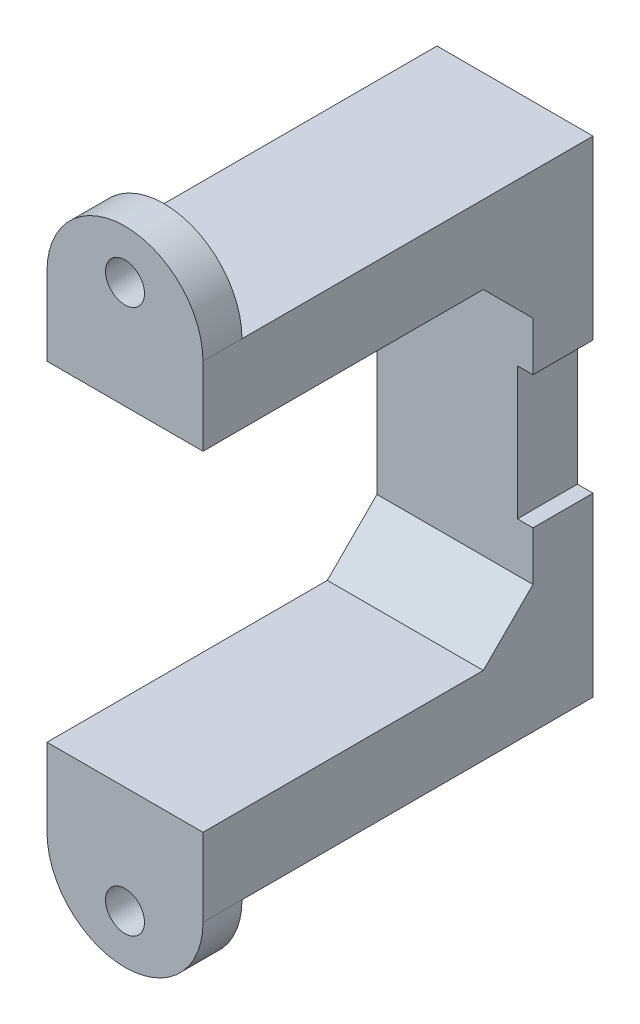
SolidWorks part; units mm, degrees
ref_plane "Ebene vorne" through (0, 0, 0) normal (0, 0, 1) x (1, 0, 0)
ref_plane "Ebene oben" through (0, 0, 0) normal (0, 1, 0) x (1, 0, 0)
ref_plane "Ebene rechts" through (0, 0, 0) normal (1, 0, 0) x (0, 0, -1)
sketch "Sketch1" plane through (0, 0, 0) normal (0, 1, 0) x (1, 0, 0)
  line L0 (-20, 0) -> (0, 0)
  line L2 (0, 0) -> (0, 50)
  line L3 (0, 50) -> (-20, 50)
  line L4 (-20, 0) -> (-20, 50)
  point P0 (0, 0)
  dimension "D1" = 20
  dimension "D2" = 50
extrude "Boss-Extrude2" add sketch "Sketch1" along normal blind 62.3
sketch "Sketch2" plane through (0, 0, 0) normal (1, 0, 0) x (0, 0, -1)
  line L1 (0, 52.3) -> (35.936, 52.3)
  line L2 (0, 52.3) -> (0, 10)
  line L3 (0, 10) -> (35.936, 10)
  line L4 (42.3, 45.936) -> (42.3, 16.364)
  line L6 (0, 62.3) -> (50, 62.3) construction
  line L7 (42.3, 16.364) -> (35.936, 10)
  line L8 (42.3, 45.936) -> (35.936, 52.3)
  line L16 (0, 62.3) -> (0, 0) construction
  point P4 (0, 0)
  dimension "D1" = 42.3
  dimension "D2" = 42.3
  dimension "D3" = 10
  dimension "D4" = 9
  dimension "D5" = 45
  dimension "D6" = 9
  dimension "D7" = 45
extrude "Cut-Extrude1" cut sketch "Sketch2" against normal through all both and the other way through all contours L2 L3 L7 L4 L8 L1
sketch "Sketch5" plane through (0, 0, 0) normal (0, 0, 1) x (1, 0, 0)
  line L0 (-20, 62.3) -> (0, 62.3)
  line L1 (-20, 62.3) -> (0, 62.3) construction
  line L2 (-20, 31.15) -> (0, 31.15) construction
  line L3 (-20, 16.364) -> (-20, 45.936) construction
  line L4 (0, 45.936) -> (0, 16.364) construction
  line L6 (-20, 62.3) -> (0, 62.3) construction
  line L7 (-20, 0) -> (0, 0)
  arc A0 (0, 62.3) -> (-20, 62.3) centre (-10, 62.3) ccw
  arc A2 (0, 0) -> (-20, 0) centre (-10, 0) cw
  point P5 (-10, 62.3)
  point P17 (0, 62.3)
extrude "Boss-Extrude3" add sketch "Sketch5" against normal blind 5
sketch "Sketch6" plane through (0, 0, -5) normal (0, 0, -1) x (-1, 0, 0)
  line L0 (0, 62.3) -> (0, 0) construction
  line L1 (0, 62.3) -> (20, 62.3) construction
  line L2 (20, 62.3) -> (0, 62.3) construction
  line L12 (0, 31.15) -> (50.2393, 31.15) construction
  circle A10 centre (10, 66.05) radius 2.5
  circle A12 centre (10, -3.75) radius 2.5
  point P6 (10, 62.3)
  point P7 (0, 31.15)
  dimension "D1" = 5
  dimension "D2" = 3.75
extrude "Cut-Extrude2" cut sketch "Sketch6" against normal blind 5
sketch "Sketch7" plane through (0, 0, -50) normal (0, 0, -1) x (-1, 0, 0)
  line L0 (0, 62.3) -> (0, 0) construction
  line L1 (0, 22.65) -> (2, 22.65)
  line L2 (0, 22.65) -> (0, 39.65)
  line L3 (0, 39.65) -> (2, 39.65)
  line L4 (2, 22.65) -> (2, 39.65)
  line L5 (0, 31.15) -> (20, 31.15) construction
  line L7 (20, 62.3) -> (20, 0) construction
  point P10 (0, 31.15)
  dimension "D1" = 17
  dimension "D2" = 2
extrude "Cut-Extrude3" cut sketch "Sketch7" against normal blind 10
